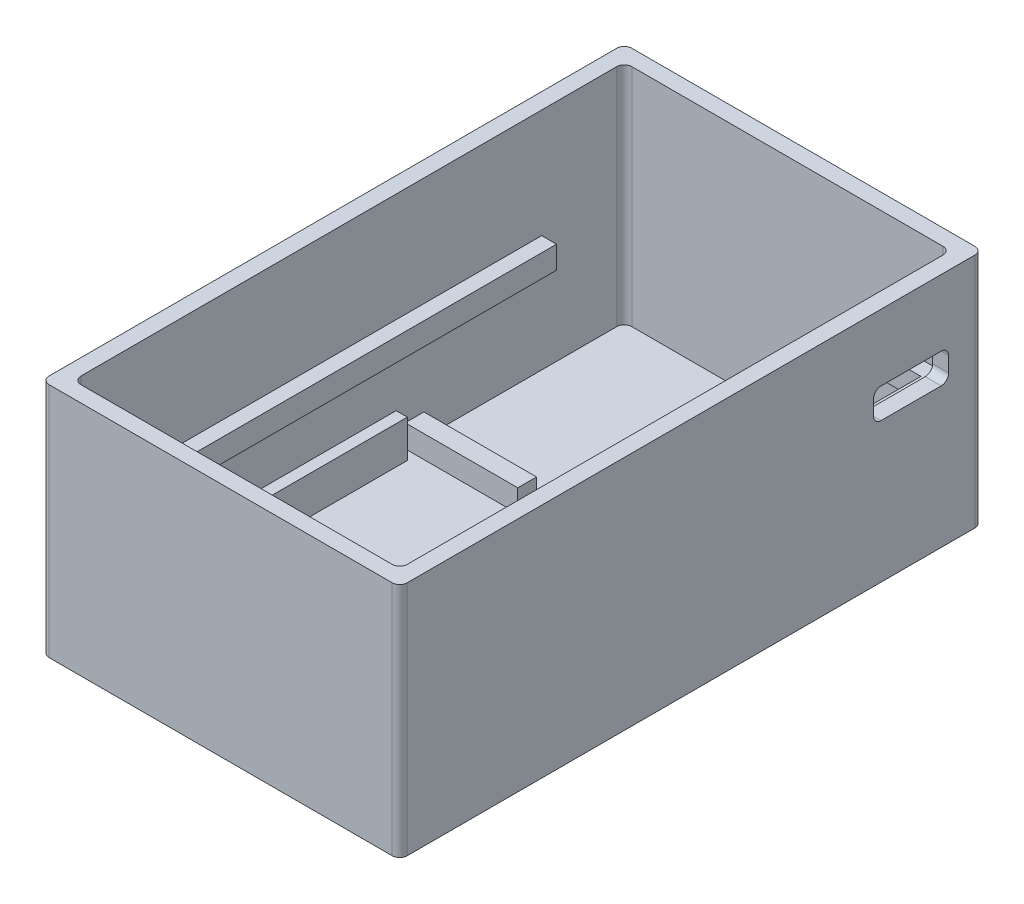
SolidWorks part; units mm, degrees
ref_plane "Front Plane" through (0, 0, 0) normal (0, 0, 1) x (1, 0, 0)
ref_plane "Top Plane" through (0, 0, 0) normal (0, 1, 0) x (1, 0, 0)
ref_plane "Right Plane" through (0, 0, 0) normal (1, 0, 0) x (0, 0, -1)
sketch "PCB Dimensions" plane through (0, 0, 0) normal (0, 1, 0) x (1, 0, 0)
  line L0 (0, 0) -> (-3.5355, 3.5355)
  line L1 (0, 0) -> (40.6457, 0)
  line L2 (0, 0) -> (0, -70.5657)
  line L3 (0, -70.5657) -> (40.6457, -70.5657)
  line L4 (40.6457, 0) -> (40.6457, -70.5657)
  line L5 (40.6457, -70.5657) -> (44.1812, -74.1012)
  line L6 (40.6457, 0) -> (44.1812, 3.5355)
  line L11 (0, -70.5657) -> (-3.5355, -74.1012)
  line L12 (44.1812, -74.1012) -> (-3.5355, -74.1012)
  line L13 (44.1812, -74.1012) -> (44.1812, 3.5355)
  line L14 (44.1812, 3.5355) -> (-3.5355, 3.5355)
  line L15 (-3.5355, -74.1012) -> (-3.5355, 3.5355)
extrude "Boss-Extrude3" add sketch "PCB Dimensions" along normal blind 1.5 contours L14 L15 L12 L13
sketch "Sketch5" plane through (0, 1.5, 0) normal (0, 1, 0) x (1, 0, 0)
  line L0 (-3.5355, 3.5355) -> (-1.4142, 1.4142)
  line L1 (-3.5355, 3.5355) -> (44.1812, 3.5355)
  line L2 (-3.5355, 3.5355) -> (-3.5355, -74.1012)
  line L7 (-3.5355, -74.1012) -> (44.1812, -74.1012)
  line L8 (44.1812, 3.5355) -> (44.1812, -74.1012)
  line L9 (44.1812, -74.1012) -> (42.0599, -71.9799)
  line L11 (-1.4142, 1.4142) -> (42.0599, 1.4142)
  line L12 (-1.4142, 1.4142) -> (-1.4142, -71.9799)
  line L13 (-1.4142, -71.9799) -> (42.0599, -71.9799)
  line L14 (42.0599, 1.4142) -> (42.0599, -71.9799)
extrude "Boss-Extrude5" add sketch "Sketch5" along normal blind 30
fillet "Fillet1" radius 1 8 edges at (42.0599, 16.5, 71.9799) (-3.5355, 15.75, 74.1012) (44.1812, 15.75, 74.1012) (44.1812, 15.75, -3.5355) (-3.5355, 15.75, -3.5355) (-1.4142, 16.5, 71.9799) (42.0599, 16.5, -1.4142) (-1.4142, 16.5, -1.4142)
sketch "Sketch9" plane through (0, 1.5, 0) normal (0, 1, 0) x (1, 0, 0)
  line L3 (0.0799, -70.9799) -> (-1.8581, -70.9799)
  line L9 (0.0799, -28.9799) -> (-1.8581, -28.9799)
  line L10 (-1.8581, -70.9799) -> (-1.8581, -28.9799)
  line L15 (42.5038, -70.9799) -> (42.5038, -28.9799)
  line L16 (40.5658, -28.9799) -> (42.5038, -28.9799)
  line L18 (40.5658, -70.9799) -> (42.5038, -70.9799)
  line L21 (0.0799, -28.9799) -> (0.0799, -70.9799)
  line L23 (40.5658, -28.9799) -> (40.5658, -70.9799)
sketch "Sketch7" plane through (0, 1.5, 0) normal (0, 1, 0) x (1, 0, 0)
  line L3 (-0.4992, 0.4992) -> (41.1449, 0.4992)
  line L4 (-0.4992, 0.4992) -> (-0.4992, -71.0649)
  line L5 (-0.4992, -71.0649) -> (41.1449, -71.0649)
  line L6 (41.1449, 0.4992) -> (41.1449, -71.0649)
extrude "Boss-Extrude6" add sketch "Sketch9" along normal blind 5 contours L21 L3 L10 L9 | L23 L18 L15 L16
sketch "Sketch14" plane through (0, 1.5, 0) normal (0, 1, 0) x (1, 0, 0)
  line L2 (-1.4142, -27.7799) -> (13.5858, -27.7799)
  line L3 (-1.4142, -27.7799) -> (-1.4142, -25.2799)
  line L4 (-1.4142, -25.2799) -> (13.5858, -25.2799)
  line L5 (13.5858, -27.7799) -> (13.5858, -25.2799)
  line L6 (27.0599, -27.7799) -> (27.0599, -25.2799)
  line L7 (42.0599, -25.2799) -> (27.0599, -25.2799)
  line L8 (42.0599, -27.7799) -> (42.0599, -25.2799)
  line L9 (42.0599, -27.7799) -> (27.0599, -27.7799)
extrude "Boss-Extrude7" add sketch "Sketch14" along normal blind 3
sketch "Sketch15" plane through (44.1812, 0, 0) normal (1, 0, 0) x (0, 0, -1)
  line L1 (-73.1012, 31.5) -> (-73.1012, 0) construction
  line L3 (2.5355, 0) -> (2.5355, 31.5) construction
  line L4 (-73.1012, 14) -> (2.5355, 14)
  line L5 (-73.1012, 14) -> (-73.1012, 17)
  line L6 (-73.1012, 17) -> (2.5355, 17)
  line L7 (2.5355, 14) -> (2.5355, 17)
  line M8 (-73.1012, 31.5) -> (-73.1012, 0)
  line M10 (2.5355, 0) -> (2.5355, 31.5)
extrude "Boss-Extrude8" add sketch "Sketch15" against normal blind 46 contours L6 L4 M8 M10
sketch "Sketch17" plane through (0, 17, 0) normal (0, 1, 0) x (1, 0, 0)
  line L3 (40.0842, -63.5437) -> (0.5614, -63.5437)
  line L4 (40.0842, -63.5437) -> (40.0842, -0.5614)
  line L5 (40.0842, -0.5614) -> (0.5614, -0.5614)
  line L6 (0.5614, -63.5437) -> (0.5614, -0.5614)
extrude "Cut-Extrude1" cut sketch "Sketch17" against normal blind 3 contours L5 L6 L3 L4
sketch "Sketch18" plane through (0, 17, 0) normal (0, 1, 0) x (1, 0, 0)
  line L0 (-1.4142, -70.9799) -> (-1.4142, 0.4142) construction
  line L1 (-1.4142, -9.5858) -> (28.5858, -9.5858)
  line L4 (28.5858, -9.5858) -> (28.5858, 1.4142)
  line L5 (-0.4142, 1.4142) -> (41.0599, 1.4142) construction
  line L6 (-0.4142, 1.4142) -> (28.5858, 1.4142)
  line L7 (-1.4142, 0.4142) -> (-1.4142, -9.5858)
  arc A0 (-1.4142, 0.4142) -> (-0.4142, 1.4142) centre (-0.4142, 0.4142) cw
extrude "Cut-Extrude2" cut sketch "Sketch18" against normal blind 3
sketch "Sketch19" plane through (44.1812, 0, 0) normal (1, 0, 0) x (0, 0, -1)
  line L0 (2.5355, 0) -> (2.5355, 17)
  line L1 (2.5355, 0) -> (2.5355, 31.5) construction
  line L2 (-0.9645, 22.65) -> (-0.9645, 18.65)
  line L11 (-0.9645, 18.65) -> (-10.9645, 18.65)
  line L13 (-0.9645, 22.65) -> (-10.9645, 22.65)
  line L14 (-10.9645, 18.65) -> (-10.9645, 22.65)
extrude "Cut-Extrude3" cut sketch "Sketch19" against normal blind 10 contours L13 L14 L11 L2
fillet "Fillet2" radius 1 4 edges at (43.1205, 18.65, 10.9645) (43.1205, 18.65, 0.9645) (43.1205, 22.65, 0.9645) (43.1205, 22.65, 10.9645)
scale "Scale1" bodies to scale 113 scale about centroid uniform scaling yes scale factor 0.99
